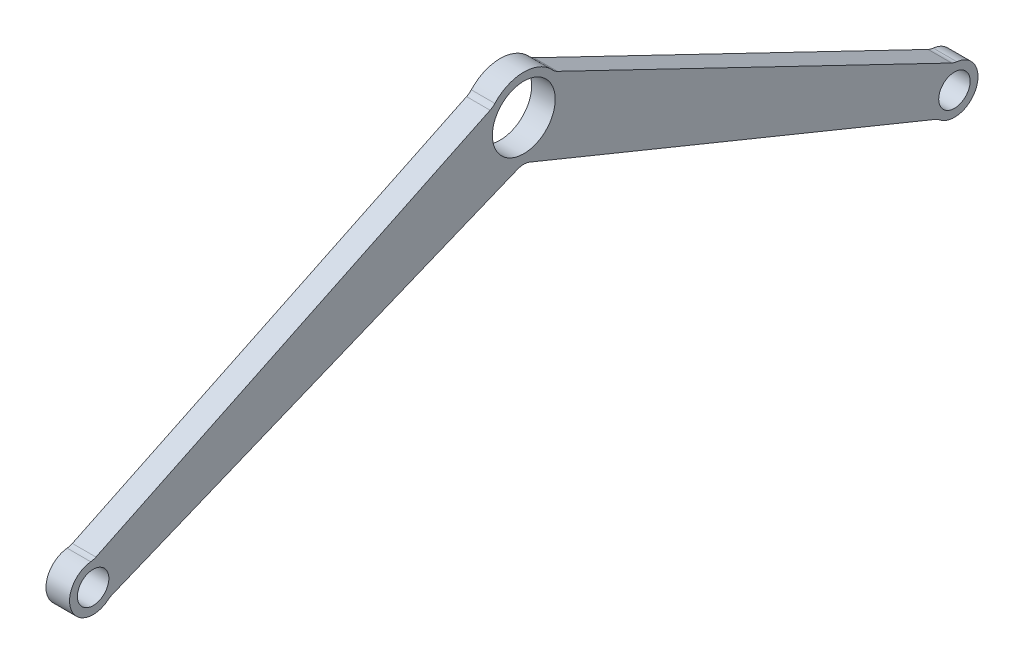
SolidWorks part; units mm, degrees
ref_plane "Front Plane" through (0, 0, 0) normal (0, 0, 1) x (1, 0, 0)
ref_plane "Top Plane" through (0, 0, 0) normal (0, 1, 0) x (1, 0, 0)
ref_plane "Right Plane" through (0, 0, 0) normal (1, 0, 0) x (0, 0, -1)
sketch "Sketch1" plane through (0, 0, 0) normal (1, 0, 0) x (0, 0, -1)
  line L0 (0, 77.2111) -> (0, -120.6041) construction
  line L1 (0, 0) -> (-548.1273, -244.042) construction
  line L2 (0, -50) -> (-548.1273, -274.042)
  line L3 (0, 50) -> (-548.1273, -214.042)
  line L4 (0, -50) -> (548.1273, -274.042)
  line L5 (0, 0) -> (548.1273, -244.042) construction
  line L6 (0, 50) -> (548.1273, -214.042)
  circle A0 centre (0, 0) radius 40
  circle A1 centre (0, 0) radius 50
  circle A2 centre (-548.1273, -244.042) radius 30
  circle A3 centre (-548.1273, -244.042) radius 20
  circle A4 centre (548.1273, -244.042) radius 20
  circle A5 centre (548.1273, -244.042) radius 30
  dimension "D1" = 100
  dimension "D2" = 80
  dimension "D5" = 60
  dimension "D6" = 40
  dimension "D3" = 600
  dimension "D4" = 66
extrude "Boss-Extrude1" add sketch "Sketch1" along normal blind 30 contours A2 L2 A1 L3 | L4 A5 L6 A1 | A3 | A0 | A4
fillet "Fillet1" radius 20 7 edges at (15, -214.042, -548.1273) (15, -265.4528, -527.1136) (15, -50, 0) (15, 31.1655, -39.0988) (15, -265.4528, 527.1136) (15, -214.042, 548.1273) (15, 31.1655, 39.0988)
